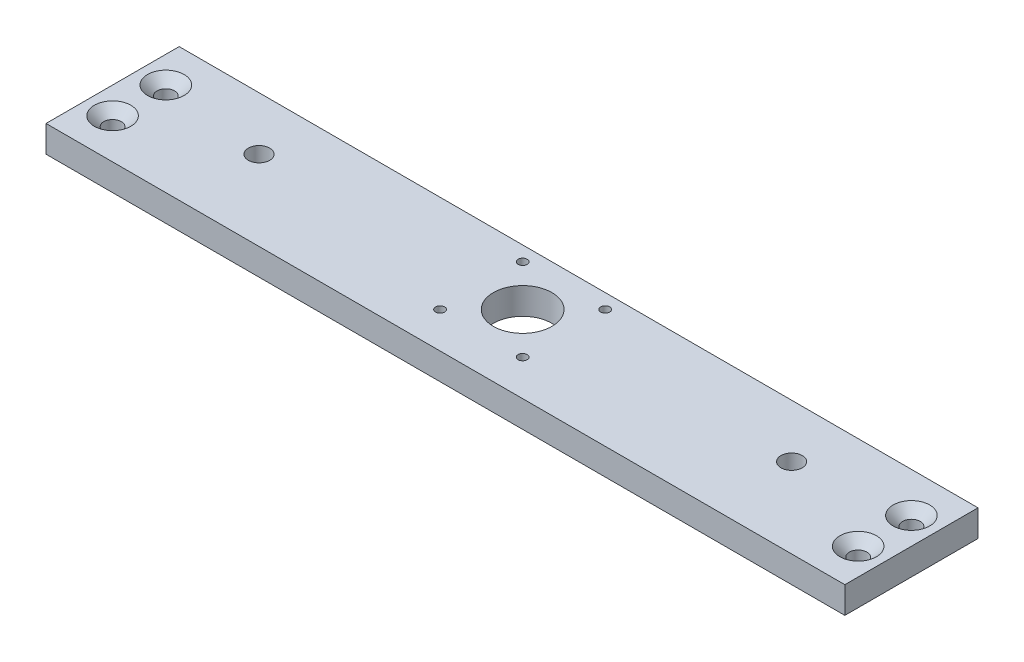
SolidWorks part; units mm, degrees
ref_plane "Front Plane" through (0, 0, 0) normal (0, 0, 1) x (1, 0, 0)
ref_plane "Top Plane" through (0, 0, 0) normal (0, 1, 0) x (1, 0, 0)
ref_plane "Right Plane" through (0, 0, 0) normal (1, 0, 0) x (0, 0, -1)
sketch "Sketch1" plane through (0, 0, 0) normal (0, 1, 0) x (1, 0, 0)
  line L0 (0, 20) -> (0, 0) construction
  line L1 (150, -30) -> (-150, -30)
  line L2 (150, -30) -> (150, 20)
  line L3 (150, 20) -> (-150, 20)
  line L4 (-150, -30) -> (-150, 20)
  line L5 (150, -30) -> (-150, 20) construction
  line L6 (150, 20) -> (-150, -30) construction
  line L7 (0, 0) -> (-100, 0) construction
  circle A0 centre (-100, 0) radius 4
  circle A1 centre (100, 0) radius 4
  point P0 (0, -5)
  dimension "D3" = 8
  dimension "D1" = 50
  dimension "D2" = 300
  dimension "D4" = 200
  dimension "D5" = 5
extrude "main" add sketch "Sketch1" along normal blind 10
sketch "Sketch4" plane through (0, 10, 0) normal (0, 1, 0) x (1, 0, 0)
  line L0 (0, 20) -> (0, -5) construction
  line L1 (150, 20) -> (-150, 20) construction
  line L2 (0, -5) -> (-150, -5) construction
  line L3 (-150, 20) -> (-150, -30) construction
  circle A0 centre (-140, 5) radius 2.5
  circle A1 centre (-140, -15) radius 2.5
  circle A2 centre (140, -15) radius 2.5
  circle A3 centre (140, 5) radius 2.5
  dimension "D1" = 5
  dimension "D2" = 10
  dimension "D3" = 20
extrude "mount" cut sketch "Sketch4" against normal through all
sketch "Sketch3" [suppressed] plane through (0, 10, 0) normal (0, 1, 0) x (1, 0, 0)
  line L0 (0, 20) -> (0, -1) construction
  line L1 (150, 20) -> (-150, 20) construction
  line L2 (0, -1) -> (-22.9552, -1) construction
  circle A0 centre (0, -1) radius 8.5
  point P2 (-100, 0)
  dimension "D1" = 17
  dimension "D2" = 1
sketch "Sketch2" plane through (0, 10, 0) normal (0, 1, 0) x (1, 0, 0)
  line L0 (0, -30) -> (0, -1) construction
  line L2 (-150, -30) -> (150, -30) construction
  line L4 (0, -1) -> (-150, -1) construction
  line L5 (-150, 20) -> (-150, -30) construction
  circle A6 centre (0, -1) radius 11
  circle A7 centre (15.5, -16.5) radius 1.5
  circle A8 centre (-15.5, -16.5) radius 1.5
  circle A9 centre (-15.5, 14.5) radius 1.5
  circle A10 centre (15.5, 14.5) radius 1.5
  point P17 (-100, 0)
  dimension "D1" = 1
  dimension "D4" = 31
  dimension "D2" = 22
  dimension "D3" = 3
  dimension "D5" = 31
extrude "stepper_mount" cut sketch "Sketch2" against normal through all
extrude "Cut-Extrude2" [suppressed] cut sketch "Sketch3" against normal through all
hole_wizard "CSK for M6 socket countersunk head screw1" positions "Sketch5" profile "Sketch6" countersink size "M6" standard "DIN"
sketch "Sketch5" plane through (0, 10, 0) normal (0, 1, 0) x (1, 0, 0)
  point P0 (140, -15)
  point P3 (140, 5)
  point P6 (-140, -15)
  point P9 (-140, 5)
sketch "Sketch6" plane through (140, 10, 15) normal (1, 0, 0) x (0, 0, 1)
  line L0 (0, 0) -> (0, 16.9828)
  line L1 (0, 16.9828) -> (3.3, 15)
  line L2 (3.3, 15) -> (3.3, 3.555)
  line L3 (3.3, 3.555) -> (6.855, 0)
  line L5 (6.855, 0) -> (0, 0)
  line L6 (-3.3, 3.555) -> (-6.855, 0) construction
  line L10 (0, 16.9828) -> (-3.3, 15) construction
  line L11 (0, -6.35) -> (0, 107.95) construction
  dimension "Hole Dia." = 6.6
  dimension "Hole Depth" = 15
  dimension "Near C'Sink Dia." = 13.71
  dimension "Near C'Sink Angle" = 90
  dimension "Drill Angle" = 118
hole_wizard "CSK for M3 socket countersunk head screw1" positions "Sketch7" profile "Sketch8" countersink size "M3" standard "DIN"
sketch "Sketch7" plane through (0, 0, 0) normal (0, -1, 0) x (-1, 0, 0)
  point P5 (15.5, -16.5)
  point P8 (-15.5, -16.5)
  point P11 (-15.5, 14.5)
  point P14 (15.5, 14.5)
sketch "Sketch8" plane through (-15.5, 0, 16.5) normal (1, 0, 0) x (0, 0, -1)
  line L0 (0, 0) -> (0, 16.0215)
  line L1 (0, 16.0215) -> (1.7, 15)
  line L2 (1.7, 15) -> (1.7, 1.77)
  line L3 (1.7, 1.77) -> (3.47, 0)
  line L5 (3.47, 0) -> (0, 0)
  line L6 (-1.7, 1.77) -> (-3.47, 0) construction
  line L10 (0, 16.0215) -> (-1.7, 15) construction
  line L11 (0, -6.35) -> (0, 107.95) construction
  dimension "Hole Dia." = 3.4
  dimension "Hole Depth" = 15
  dimension "Near C'Sink Dia." = 6.94
  dimension "Near C'Sink Angle" = 90
  dimension "Drill Angle" = 118
